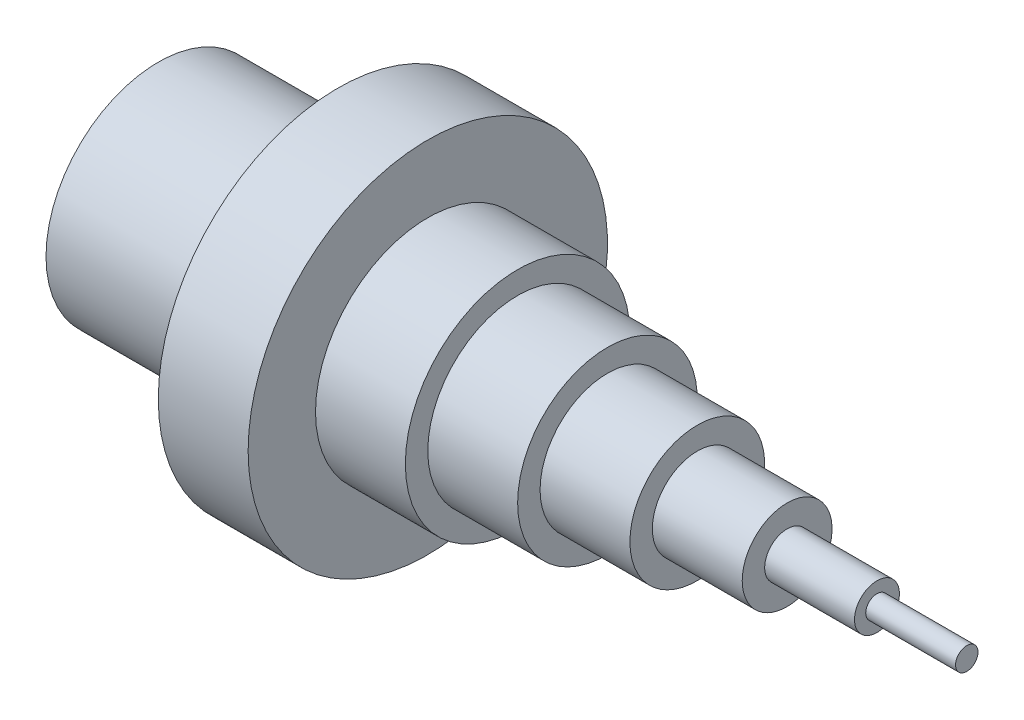
SolidWorks part; units mm, degrees
ref_plane "Front Plane" through (0, 0, 0) normal (0, 0, 1) x (1, 0, 0)
ref_plane "Top Plane" through (0, 0, 0) normal (0, 1, 0) x (1, 0, 0)
ref_plane "Right Plane" through (0, 0, 0) normal (1, 0, 0) x (0, 0, -1)
sketch "Sketch2" plane through (0, 0, 0) normal (0, 0, 1) x (1, 0, 0)
  line L0 (0, 0) -> (2842.8969, 0) construction
  line L1 (400, 0) -> (400, 200)
  line L2 (400, 200) -> (0, 200)
  line L3 (0, 200) -> (0, 250)
  line L4 (0, 250) -> (400, 250)
  line L5 (400, 250) -> (400, 400)
  line L6 (400, 400) -> (600, 400)
  line L7 (600, 400) -> (600, 250)
  line L8 (600, 250) -> (800, 250)
  line L9 (800, 250) -> (800, 200)
  line L10 (800, 200) -> (1000, 200)
  line L11 (1000, 200) -> (1000, 150)
  line L12 (1000, 150) -> (1200, 150)
  line L13 (1200, 150) -> (1200, 100)
  line L14 (1200, 100) -> (1400, 100)
  line L15 (1400, 100) -> (1400, 50)
  line L16 (1600, 50) -> (1600, 25)
  line L17 (1600, 25) -> (1800, 25)
  line L18 (1800, 25) -> (1800, 0)
  line L19 (1800, 0) -> (400, 0)
  line L20 (400, 0) -> (389.9721, -7.5209)
  line L21 (1600, 50) -> (1400, 50)
  line L22 (389.9721, -7.5209) -> (1800, 0)
  dimension "D1" = 1800
  dimension "D2" = 50
  dimension "D3" = 100
  dimension "D4" = 200
  dimension "D5" = 300
  dimension "D6" = 400
  dimension "D7" = 500
  dimension "D8" = 800
  dimension "D9" = 400
  dimension "D10" = 500
  dimension "D11" = 400
revolve "Revolve6" add sketch "Sketch2" angle 360 about L0
